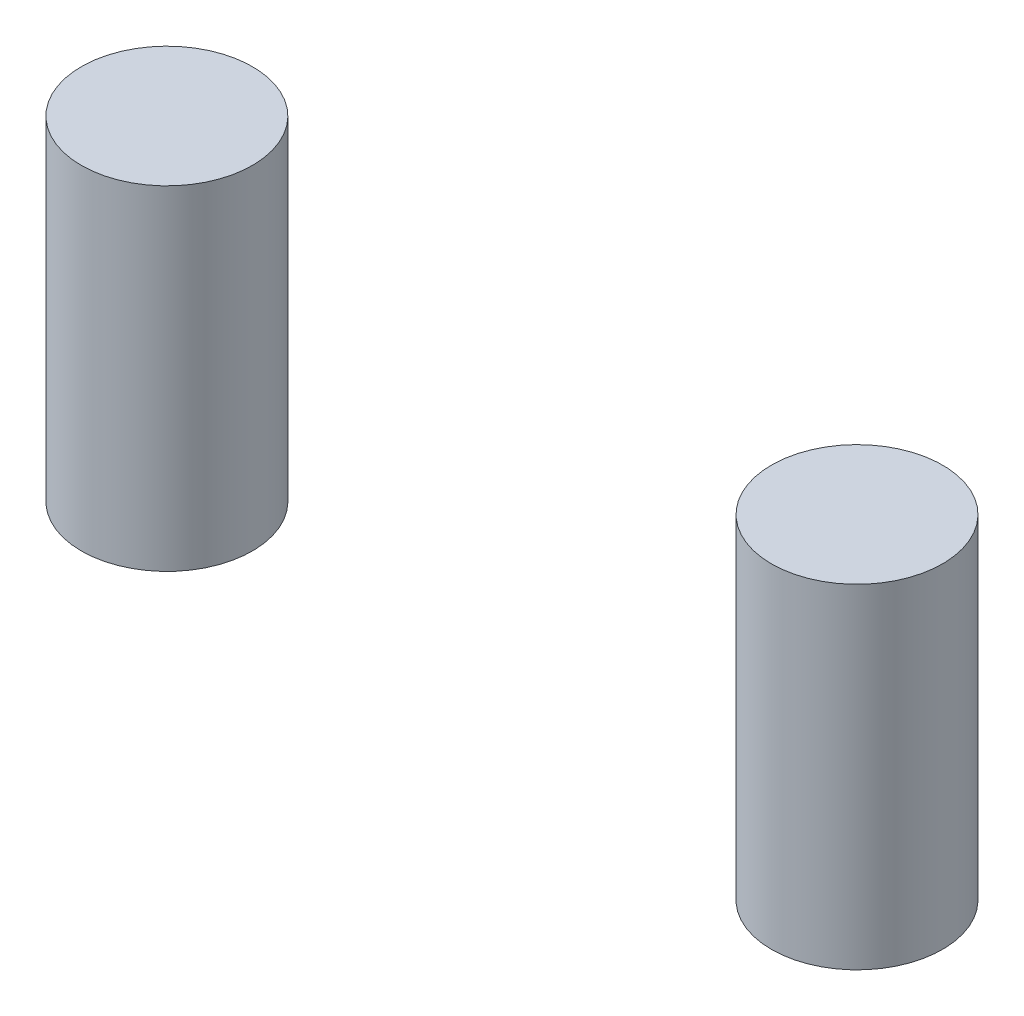
SolidWorks part; units mm, degrees
ref_plane "Front Plane" through (0, 0, 0) normal (0, 0, 1) x (1, 0, 0)
ref_plane "Top Plane" through (0, 0, 0) normal (0, 1, 0) x (1, 0, 0)
ref_plane "Right Plane" through (0, 0, 0) normal (1, 0, 0) x (0, 0, -1)
sketch "Sketch1" plane through (0, 0, 0) normal (0, 1, 0) x (1, 0, 0)
  circle A0 centre (3.1, -3.1) radius 3.075
  circle A1 centre (27.9, -3.1) radius 3.075
  dimension "D1" = 6.15
  dimension "D2" = 6.15
  dimension "D3" = 24.8
extrude "Boss-Extrude1" add sketch "Sketch1" along normal blind 12
